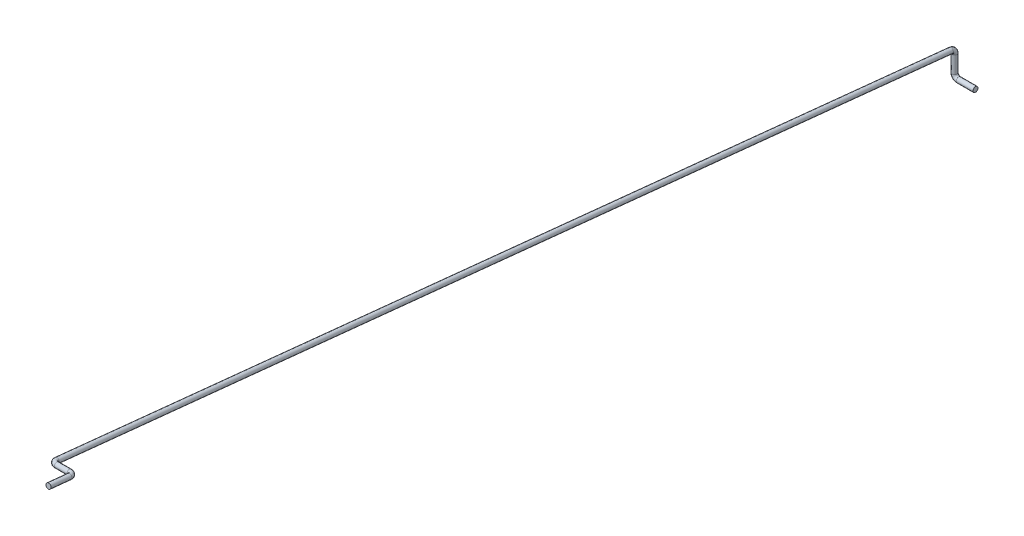
SolidWorks part; units mm, degrees
material "Alloy Steel"
ref_plane "Front" through (0, 0, 0) normal (0, 0, 1) x (1, 0, 0)
ref_plane "Top" through (0, 0, 0) normal (0, 1, 0) x (1, 0, 0)
ref_plane "Right" through (0, 0, 0) normal (1, 0, 0) x (0, 0, -1)
sketch "Sketch1" plane through (0, 0, 0) normal (1, 0, 0) x (0, 0, -1)
  line L0 (0, 0) -> (0, 2)
  line L1 (-0.8978, 2.9948) -> (-214.0052, 24.8978)
  line L2 (0, 0) -> (-215, 0) construction
  line L3 (-215, 0) -> (-215, 25) construction
  line L4 (-215, 25) -> (-214.0052, 24.8978) construction
  arc A1 (0, 2) -> (-0.8978, 2.9948) centre (-1, 2) ccw
  dimension "D1" = 1
  dimension "D2" = 2
  dimension "D3" = 25
  dimension "D4" = 215
  dimension "D5" = 1
sketch "Sketch2" plane through (0, 0, 0) normal (0, 1, 0) x (1, 0, 0)
  circle A0 centre (0, 0) radius 0.6
  dimension "D1" = 1.2
sweep "Sweep1" add profiles "Sketch2" path "Sketch1"
sketch "Sketch4" plane through (0, 0, 0) normal (0, 0, 1) x (1, 0, 0)
  line L0 (0, 0) -> (0, -2)
  line L1 (1, -3) -> (5, -3)
  arc A0 (0, -2) -> (1, -3) centre (1, -2) ccw
  dimension "D2" = 1
  dimension "D1" = 2
  dimension "D3" = 4
sketch "Sketch6" plane through (0, 0, 0) normal (0, -1, 0) x (1, 0, 0)
  circle A1 centre (0, 0) radius 0.6
  circle A2 centre (0, 0) radius 0.6
  dimension "D1" = 0
sweep "Sweep3" add profiles "Sketch6" path "Sketch4"
ref_plane "Plane1" through (0, 0, 215) normal (0, 0, 1) x (1, 0, 0)
sketch "Sketch7" plane through (0, 0, 215) normal (0, 0, 1) x (1, 0, 0)
  line L0 (0, 25) -> (-30, 25) construction
  dimension "D1" = 30
ref_plane "Plane2" through (0, 2.8721, -0.2952) normal (0, -0.9948, 0.1022) x (1, 0, 0)
sketch "Sketch8" plane through (0, 2.8721, -0.2952) normal (0, -0.9948, 0.1022) x (1, 0, 0)
  line L0 (-4, 216.4294) -> (-1, 216.4294)
  line L1 (-5, 217.4294) -> (-5, 222.4294)
  line L2 (0, 1.1992) -> (0, 215.4294) construction
  arc A0 (-1, 216.4294) -> (0, 215.4294) centre (-1, 215.4294) cw
  arc A1 (-4, 216.4294) -> (-5, 217.4294) centre (-4, 217.4294) cw
  point P10 (-2.5, 216.4294)
  dimension "D1" = 1
  dimension "D2" = 5
  dimension "D3" = 3
sketch "Sketch9" plane through (0, 2.8721, -0.2952) normal (0, -0.9948, 0.1022) x (1, 0, 0)
  line L0 (5, 222.4294) -> (5, 217.4294)
  line L1 (4, 216.4294) -> (1, 216.4294)
  line L2 (0, 1.1992) -> (0, 215.4294) construction
  line L3 (-4, 216.4294) -> (-1, 216.4294) construction
  line L4 (-5, 217.4294) -> (-5, 222.4294) construction
  arc A0 (5, 217.4294) -> (4, 216.4294) centre (4, 217.4294) cw
  arc A1 (1, 216.4294) -> (0, 215.4294) centre (1, 215.4294) ccw
  arc A2 (0, 215.4294) -> (-1, 216.4294) centre (-1, 215.4294) ccw construction
  point P17 (2.5, 216.4294)
sketch "Sketch10" plane through (0, 22.0256, 214.3004) normal (0, 0.1022, 0.9948) x (1, 0, 0)
  circle A1 centre (0, 2.8873) radius 0.6
  circle A2 centre (0, 2.8873) radius 0.6
  dimension "D1" = 0
sketch "Sketch11" plane through (0, 22.0256, 214.3004) normal (0, 0.1022, 0.9948) x (1, 0, 0)
  circle A0 centre (0, 2.8873) radius 0.6
  dimension "D1" = 1.2
sweep "Sweep4" add profiles "Sketch10" path "Sketch9"
sweep "Sweep5" add profiles "Sketch11" path "Sketch8"
